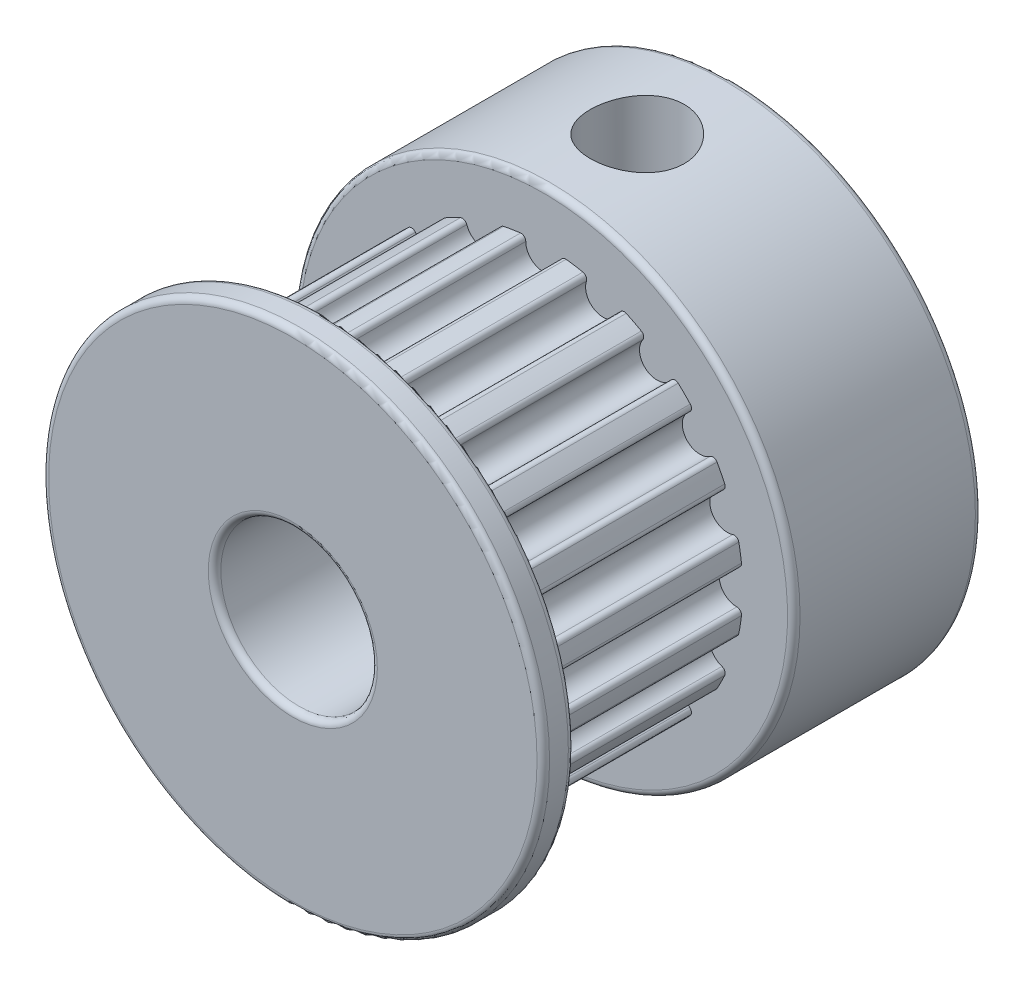
SolidWorks part; units mm, degrees
ref_plane "Ön Düzlem" through (0, 0, 0) normal (0, 0, 1) x (1, 0, 0)
ref_plane "Üst Düzlem" through (0, 0, 0) normal (0, 1, 0) x (1, 0, 0)
ref_plane "Sağ Düzlem" through (0, 0, 0) normal (1, 0, 0) x (0, 0, -1)
sketch "Çizim1" plane through (0, 0, 0) normal (0, 0, 1) x (1, 0, 0)
  circle A0 centre (0, 0) radius 6.37
  circle A1 centre (0, 0) radius 2.5
extrude "Yükseklik-Ekstrüzyon1" add sketch "Çizim1" along normal blind 7
sketch "Çizim2" plane through (0, 0, 7) normal (0, 0, 1) x (1, 0, 0)
  arc A3 (-0.5343, 6.3475) -> (0.5343, 6.3475) centre (0, 6.18) ccw
  arc A4 (0.5343, 6.3475) -> (-0.5343, 6.3475) centre (0, 0) ccw
extrude "Kes-Ekstrüzyon2" cut sketch "Çizim2" against normal blind 7 contours A3 A4
fillet "Radyus2" radius 0.15 2 edges at (0.5343, 6.3475, 3.5) (-0.5343, 6.3475, 3.5)
pattern_circular "Dairesel Kaplama2" count 20 over 360 about axis through (0, 0, 0) along (0, 0, 1) of "Kes-Ekstrüzyon2", "Radyus2"
sketch "Çizim4" plane through (0, 0, 7) normal (0, 0, 1) x (1, 0, 0)
  circle A0 centre (0, 0) radius 2.5
  circle A1 centre (0, 0) radius 8
extrude "Yükseklik-Ekstrüzyon2" add sketch "Çizim4" along normal blind 1
sketch "Çizim5" plane through (0, 0, 0) normal (0, 0, -1) x (-1, 0, 0)
  circle A0 centre (0, 0) radius 2.5
  circle A1 centre (0, 0) radius 8
extrude "Yükseklik-Ekstrüzyon4" add sketch "Çizim5" along normal blind 6
fillet "Radyus3" radius 0.2 6 edges at (8, 0, 7) (-8, 0, 0) (-2.5, 0, -6) (-8, 0, -6) (2.5, 0, 8) (8, 0, 8)
ref_plane "Düzlem1" through (0, 10, 0) normal (0, 1, 0) x (1, 0, 0)
sketch "Çizim6" plane through (0, 10, 0) normal (0, 1, 0) x (1, 0, 0)
  circle A0 centre (0, 3) radius 1.5
extrude "Kes-Ekstrüzyon3" cut sketch "Çizim6" against normal blind 10
